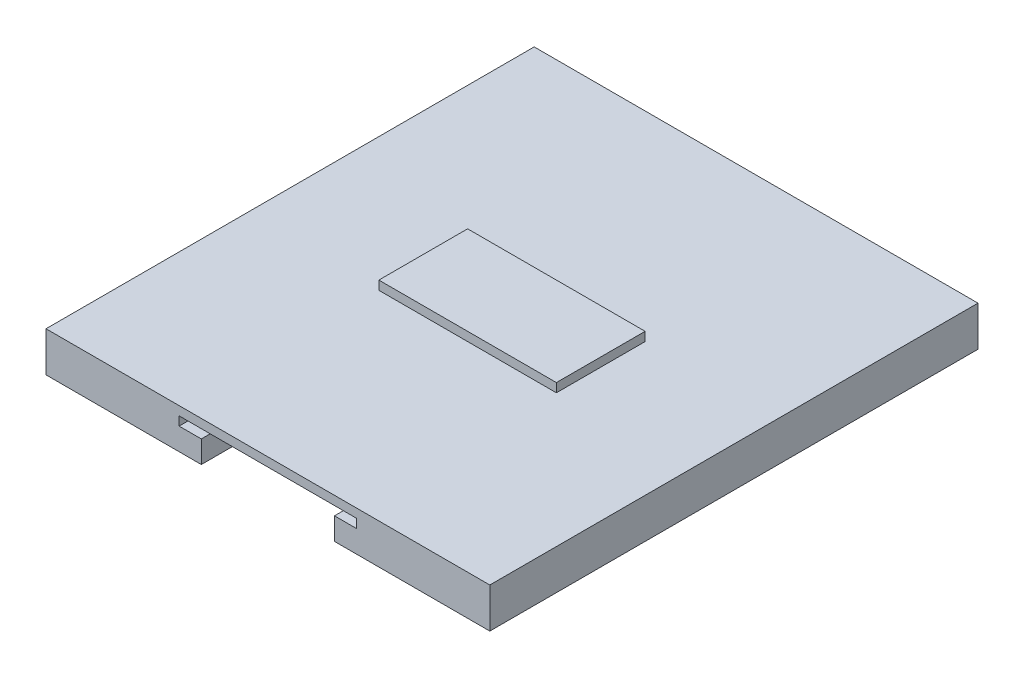
SolidWorks part; units mm, degrees
material "Chrome Stainless Steel"
ref_plane "Front Plane" through (0, 0, 0) normal (0, 0, 1) x (1, 0, 0)
ref_plane "Top Plane" through (0, 0, 0) normal (0, 1, 0) x (1, 0, 0)
ref_plane "Right Plane" through (0, 0, 0) normal (1, 0, 0) x (0, 0, -1)
other "Configuration Table"
sketch "Sketch2" plane through (0, 0, 0) normal (0, 0, -1) x (-1, 0, 0)
  line L1 (50, 9) -> (-50, 9)
  line L2 (50, 9) -> (50, 0)
  line L3 (50, 0) -> (-50, 0)
  line L4 (-50, 9) -> (-50, 0)
  dimension "D1" = 100
  dimension "D2" = 9
extrude "Extrude1" add sketch "Sketch2" against normal mid plane 110
sketch "Sketch5" plane through (0, 0, -55) normal (0, 0, -1) x (-1, 0, 0)
  line L7 (20, 5) -> (20, 7)
  line L8 (15, 5) -> (20, 5)
  line L9 (15, 0) -> (15, 5)
  line L10 (-15, 5) -> (-15, 0)
  line L11 (-20, 5) -> (-15, 5)
  line L12 (20, 7) -> (-20, 7)
  line L13 (-20, 7) -> (-20, 5)
  line L14 (-15, 0) -> (15, 0)
  line L15 (0, 0) -> (0, 17.2115) construction
  dimension "D1" = 30
  dimension "D2" = 5
  dimension "D3" = 2
  dimension "D4" = 40
extrude "Cut-Extrude1" cut sketch "Sketch5" against normal through all
sketch "Sketch6" plane through (0, 0, -55) normal (0, 0, -1) x (-1, 0, 0)
  line L0 (0, 15.0009) -> (0, 0)
split line "Split Line1" [suppressed]
sketch "Sketch7" plane through (0, 9, 0) normal (0, 1, 0) x (1, 0, 0)
  line L0 (20, 10) -> (-20, -10) construction
  line L1 (-20, 10) -> (20, 10)
  line L2 (-20, 10) -> (-20, -10)
  line L3 (-20, -10) -> (20, -10)
  line L4 (20, 10) -> (20, -10)
  dimension "D1" = 40
  dimension "D2" = 20
extrude "Extrude2" add sketch "Sketch7" along normal blind 2
